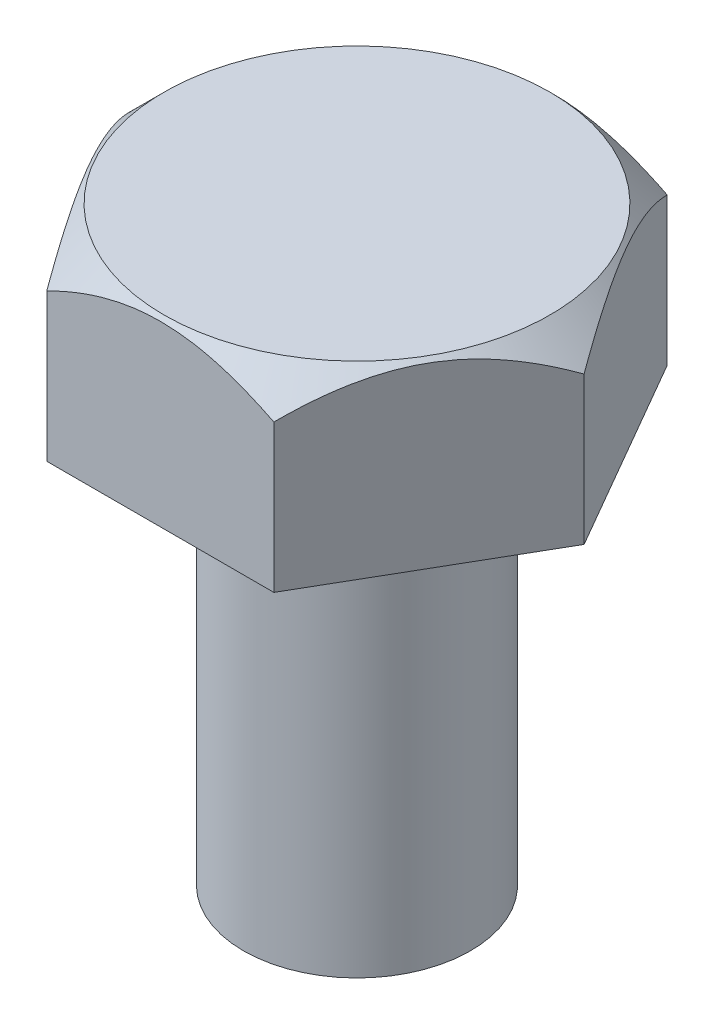
SolidWorks part; units mm, degrees
ref_plane "Front Plane" through (0, 0, 0) normal (0, 0, 1) x (1, 0, 0)
ref_plane "Top Plane" through (0, 0, 0) normal (0, 1, 0) x (1, 0, 0)
ref_plane "Right Plane" through (0, 0, 0) normal (1, 0, 0) x (0, 0, -1)
sketch "Sketch1" plane through (0, 0, 0) normal (0, 1, 0) x (1, 0, 0)
  circle A0 centre (0, 0) radius 2.5
  dimension "D1" = 5
extrude "Boss-Extrude1" add sketch "Sketch1" along normal blind 9
sketch "Sketch3" plane through (0, 9, 0) normal (0, 1, 0) x (1, 0, 0)
  line L1 (5, 0) -> (2.5, 4.3301)
  line L2 (2.5, 4.3301) -> (-2.5, 4.3301)
  line L3 (-2.5, 4.3301) -> (-5, 0)
  line L4 (-5, 0) -> (-2.5, -4.3301)
  line L5 (-2.5, -4.3301) -> (2.5, -4.3301)
  line L6 (2.5, -4.3301) -> (5, 0)
  line L7 (0, 6.9502) -> (0, -10.3619) construction
  circle A0 centre (0, 0) radius 4.3301 construction
  dimension "D1" = 10
extrude "Boss-Extrude4" add sketch "Sketch3" along normal blind 4
sketch "Sketch5" plane through (0, 13, 0) normal (0, 1, 0) x (1, 0, 0)
  circle A0 centre (0, 0) radius 4.25
  dimension "D1" = 8.5
extrude "Cut-Extrude1" cut sketch "Sketch5" against normal blind 4 draft 45 flip side to cut
